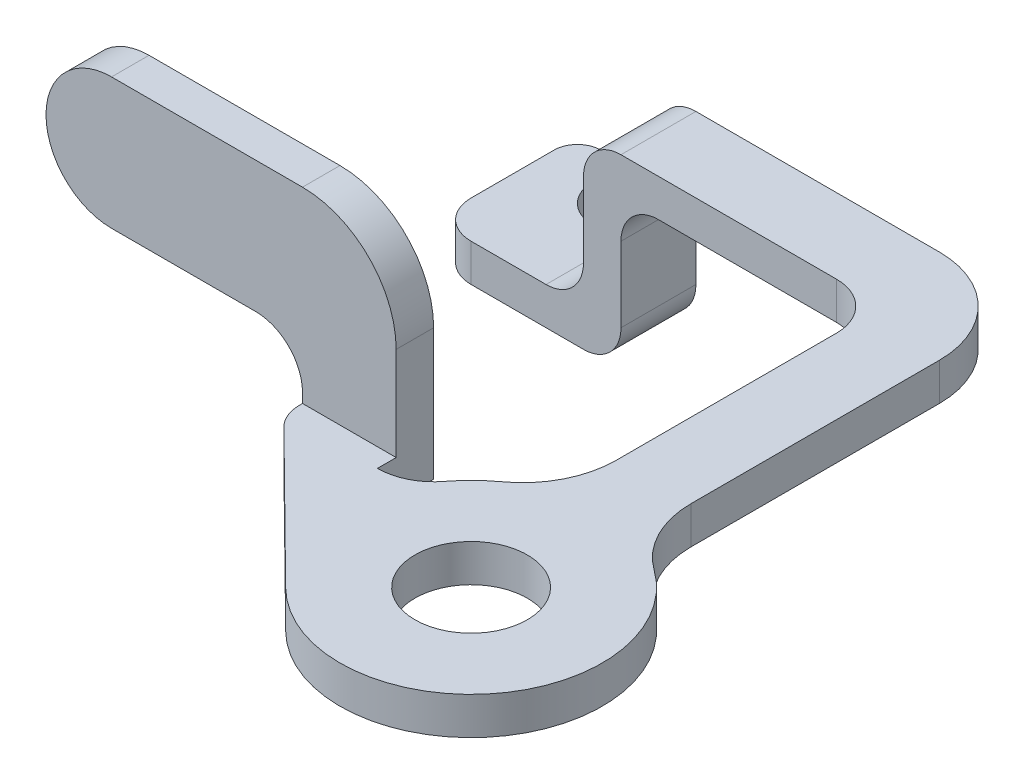
SolidWorks part; units mm, degrees
ref_plane "Planta" through (0, 0, 0) normal (0, 0, 1) x (1, 0, 0)
ref_plane "Alzado" through (0, 0, 0) normal (0, 1, 0) x (1, 0, 0)
ref_plane "Vista lateral" through (0, 0, 0) normal (1, 0, 0) x (0, 0, -1)
sketch "Croquis1" plane through (0, 0, 0) normal (0, 1, 0) x (1, 0, 0)
  line L0 (0, 0) -> (0, 3) construction
  line L1 (2, 16.626) -> (2, 6.7082)
  line L2 (-2, 24) -> (-2, 6.7082)
  line L3 (2, 16.626) -> (2, 28)
  line L4 (2, 28) -> (-16, 28)
  line L5 (-16, 28) -> (-16, 24)
  line L6 (-16, 24) -> (-2, 24)
  line L7 (-8, 3) -> (-31.5734, 3) construction
  line L8 (-8, 3) -> (-8, 4)
  line L9 (-8, 4) -> (-13, 4)
  line L10 (-13, 4) -> (-13, 3)
  line L11 (-13, 3) -> (-4.9186, -4.9807)
  arc A0 (-2, 6.7082) -> (-5.6, 4.2) centre (0, 0) ccw
  circle A1 centre (0, 0) radius 3
  arc A2 (-8, 3) -> (-5.6, 4.2) centre (-8, 6) ccw
  arc A3 (-4.9186, -4.9807) -> (2, 6.7082) centre (0, 0) ccw
  dimension "D1" = 14
  dimension "D2" = 6
  dimension "D3" = 4
  dimension "D4" = 2
  dimension "D5" = 2
  dimension "D6" = 28
  dimension "D7" = 8
  dimension "D8" = 1
  dimension "D9" = 5
  dimension "D10" = 18
extrude "Saliente-Extruir1" add sketch "Croquis1" along normal blind 2
sketch "Croquis2" plane through (0, 0, -4) normal (0, 0, -1) x (-1, 0, 0)
  line L0 (8, 2) -> (8, 12)
  line L1 (8, 12) -> (23.1925, 12)
  line L2 (8, 0) -> (13, 0) construction
  line L3 (23.1925, 5) -> (13, 5)
  line L4 (13, 5) -> (13, 2)
  line L5 (8, 2) -> (8, 0) construction
  line L6 (13, 2) -> (13, 0) construction
  line L7 (8, 2) -> (13, 2) construction
  line L8 (13, 2) -> (13, 0)
  line L9 (8, 0) -> (13, 0)
  line L10 (8, 2) -> (8, 0)
  arc A0 (23.1925, 5) -> (23.1925, 12) centre (23.1925, 8.5) ccw
  dimension "D1" = 10
extrude "Saliente-Extruir2" add sketch "Croquis2" along normal blind 2
fillet "Redondeo1" radius 5 1 edges at (-8, 12, -5)
fillet "Redondeo2" radius 2.5 1 edges at (-13, 5, -5)
fillet "Redondeo3" radius 5 1 edges at (2, 1, -6.7082)
fillet "Redondeo4" radius 5 1 edges at (-2, 1, -6.7082)
fillet "Redondeo5" radius 2 1 edges at (-13, 1, -3)
fillet "Redondeo6" radius 5 1 edges at (2, 1, -28)
fillet "Redondeo7" radius 2.5 1 edges at (-2, 1, -24)
sketch "Croquis3" plane through (0, 0, -28) normal (0, 0, -1) x (-1, 0, 0)
  line L0 (-2, 0) -> (-2, 2) construction
  line L1 (-2, 0) -> (-2, 2)
  line L2 (16, 2) -> (16, 0) construction
  line L3 (16, 2) -> (16, 0)
  line L4 (18, 0) -> (18, -6)
  line L5 (16, 0) -> (16, -6)
  line L6 (18, -8) -> (26, -8)
  line L7 (26, -8) -> (26, -6)
  line L8 (26, -6) -> (18, -6)
  arc A0 (18, 0) -> (16, 2) centre (16, 0) ccw
  arc A1 (16, -6) -> (18, -8) centre (18, -6) ccw
  dimension "D1" = 4
  dimension "D2" = 2
  dimension "D5" = 4
  dimension "D4" = 2
extrude "Saliente-Extruir3" add sketch "Croquis3" against normal blind 4 contours L3 L5 A1 L6 L7 L8 L4 A0
fillet "Redondeo8" radius 2 1 edges at (-18, -6, -26)
fillet "Redondeo9" radius 2 1 edges at (-16, 0, -26)
sketch "Croquis4" plane through (0, -6, 0) normal (0, 1, 0) x (1, 0, 0)
  line L0 (-23.5, 28) -> (-23.5, 30.5)
  line L1 (-26, 28) -> (-20, 28) construction
  line L2 (-26, 28) -> (-26, 30.5)
  line L3 (-26, 28) -> (-23.5, 28)
  arc A0 (-23.5, 30.5) -> (-26, 30.5) centre (-24.75, 30.4258) ccw
  dimension "D1" = 2.5
  dimension "D2" = 2.5
  dimension "D3" = 2.5
extrude "Saliente-Extruir4" add sketch "Croquis4" against normal blind 2
fillet "Redondeo10" radius 2 1 edges at (-23.5, -7, -28)
sketch "Croquis5" plane through (0, -6, 0) normal (0, 1, 0) x (1, 0, 0)
  line L0 (-26, 24) -> (-26, 30.5) construction
  line L1 (-26, 24) -> (-26, 26)
  line L2 (-26, 24) -> (-20, 24) construction
  line L3 (-26, 24) -> (-24, 24)
  arc A0 (-26, 26) -> (-24, 24) centre (-24, 26) ccw
  dimension "D1" = 2
extrude "Cortar-Extruir1" cut sketch "Croquis5" against normal blind 2
